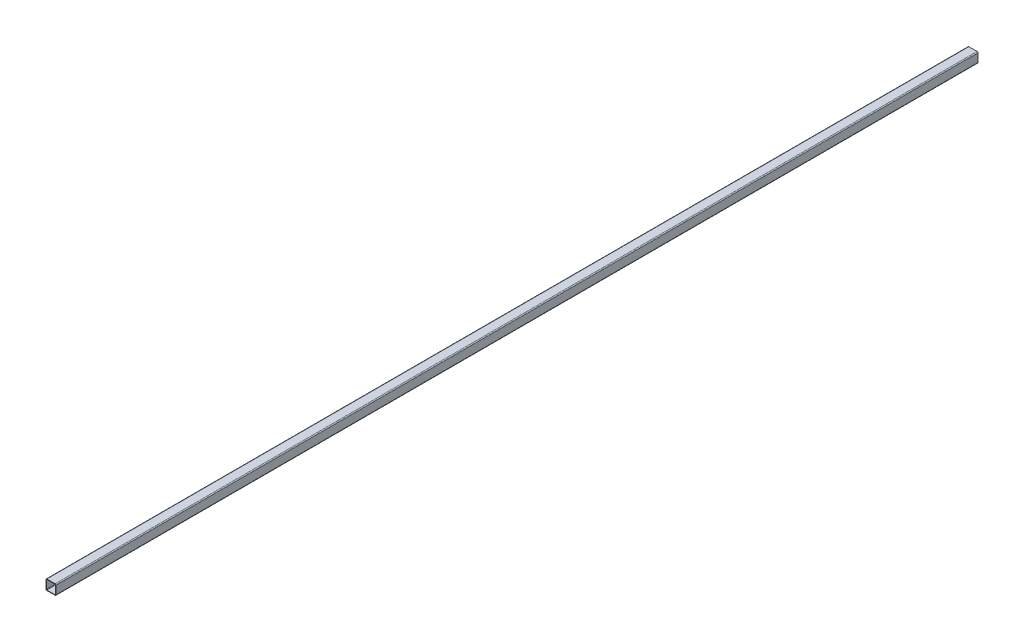
SolidWorks part; units mm, degrees
material "Thornel Mat VMA"
ref_plane "Front Plane" through (0, 0, 0) normal (0, 0, 1) x (1, 0, 0)
ref_plane "Top Plane" through (0, 0, 0) normal (0, 1, 0) x (1, 0, 0)
ref_plane "Right Plane" through (0, 0, 0) normal (1, 0, 0) x (0, 0, -1)
sketch "Sketch1" plane through (0, 0, 0) normal (0, 0, 1) x (1, 0, 0)
  line L0 (-12.5603, 11.2903) -> (-12.5603, -11.2903)
  line L1 (-11.2903, 13.8303) -> (11.2903, 13.8303)
  line L2 (-13.8303, 11.2903) -> (-13.8303, -11.2903)
  line L3 (-11.2903, -13.8303) -> (11.2903, -13.8303)
  line L4 (13.8303, 11.2903) -> (13.8303, -11.2903)
  line L5 (-11.2903, -12.5603) -> (11.2903, -12.5603)
  line L6 (12.5603, 11.2903) -> (12.5603, -11.2903)
  line L7 (-11.2903, 12.5603) -> (11.2903, 12.5603)
  arc A0 (-13.8303, -11.2903) -> (-11.2903, -13.8303) centre (-11.2903, -11.2903) ccw
  arc A1 (11.2903, -13.8303) -> (13.8303, -11.2903) centre (11.2903, -11.2903) ccw
  arc A2 (11.2903, 13.8303) -> (13.8303, 11.2903) centre (11.2903, 11.2903) cw
  arc A3 (-11.2903, 13.8303) -> (-13.8303, 11.2903) centre (-11.2903, 11.2903) ccw
  arc A4 (-12.5603, -11.2903) -> (-11.2903, -12.5603) centre (-11.2903, -11.2903) ccw
  arc A5 (11.2903, -12.5603) -> (12.5603, -11.2903) centre (11.2903, -11.2903) ccw
  arc A6 (11.2903, 12.5603) -> (12.5603, 11.2903) centre (11.2903, 11.2903) cw
  arc A7 (-11.2903, 12.5603) -> (-12.5603, 11.2903) centre (-11.2903, 11.2903) ccw
  point P4 (0, 13.8303)
  point P6 (13.8303, 0)
  point P13 (13.8303, 13.8303)
  point P16 (-13.8303, 13.8303)
  dimension "D2" = 2.54
  dimension "D1" = 27.6606
  dimension "D3" = 1.27
extrude "Boss-Extrude1" add sketch "Sketch1" along normal mid plane 2540
